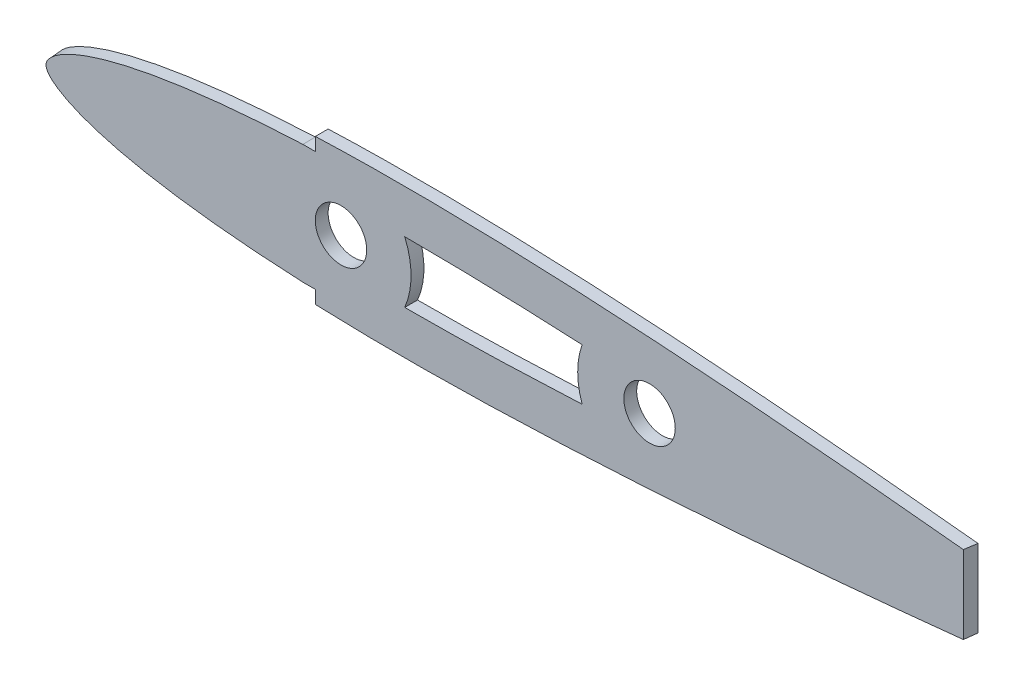
SolidWorks part; units mm, degrees
material "Balsa"
ref_plane "Front Plane" through (0, 0, 0) normal (0, 0, 1) x (1, 0, 0)
ref_plane "Top Plane" through (0, 0, 0) normal (0, 1, 0) x (1, 0, 0)
ref_plane "Right Plane" through (0, 0, 0) normal (1, 0, 0) x (0, 0, -1)
curve "Curve1"
  spline degree 3 poles (306.1523, -0.5171, 0) (306.1523, 0.5171, 0) (305.121, 0.3908, 0) (303.8142, 0.7587, 0) (301.4178, 0.9861, 0) (298.1894, 1.474, 0) (294.0308, 2.0185, 0) (289.0158, 2.6897, 0) (283.1575, 3.4483, 0) (276.4981, 4.2929, 0) (269.0768, 5.2087, 0) (260.9399, 6.1834, 0) (252.1374, 7.2048, 0) (242.7235, 8.259, 0) (232.7563, 9.3331, 0) (222.2974, 10.4139, 0) (211.4111, 11.4873, 0) (200.1646, 12.5383, 0) (188.6272, 13.5531, 0) (176.8702, 14.5147, 0) (164.9658, 15.4075, 0) (152.9874, 16.2149, 0) (141.009, 16.9199, 0) (129.1042, 17.5048, 0) (117.3465, 17.954, 0) (105.8081, 18.2528, 0) (94.5604, 18.3867, 0) (83.6724, 18.345, 0) (73.2112, 18.1196, 0) (63.2413, 17.7049, 0) (53.824, 17.0997, 0) (45.0172, 16.3058, 0) (36.8748, 15.3296, 0) (29.4464, 14.1792, 0) (22.777, 12.8667, 0) (16.9057, 11.407, 0) (11.866, 9.8142, 0) (7.6833, 8.1032, 0) (4.371, 6.2856, 0) (1.9343, 4.3578, 0) (0.3736, 2.2731, 0) (-0.1741, 0, 0) (0.3736, -2.2731, 0) (1.9343, -4.3578, 0) (4.371, -6.2856, 0) (7.6833, -8.1032, 0) (11.866, -9.8142, 0) (16.9057, -11.407, 0) (22.777, -12.8667, 0) (29.4464, -14.1792, 0) (36.8748, -15.3296, 0) (45.0172, -16.3058, 0) (53.824, -17.0997, 0) (63.2413, -17.7049, 0) (73.2112, -18.1196, 0) (83.6724, -18.345, 0) (94.5604, -18.3867, 0) (105.8081, -18.2528, 0) (117.3465, -17.954, 0) (129.1042, -17.5048, 0) (141.009, -16.9199, 0) (152.9874, -16.2149, 0) (164.9658, -15.4075, 0) (176.8702, -14.5147, 0) (188.6272, -13.5531, 0) (200.1646, -12.5383, 0) (211.4111, -11.4873, 0) (222.2974, -10.4139, 0) (232.7563, -9.3331, 0) (242.7235, -8.259, 0) (252.1374, -7.2048, 0) (260.9399, -6.1834, 0) (269.0768, -5.2087, 0) (276.4981, -4.2929, 0) (283.1575, -3.4483, 0) (289.0158, -2.6897, 0) (294.0308, -2.0185, 0) (298.1894, -1.474, 0) (301.4178, -0.9861, 0) (303.8142, -0.7587, 0) (305.121, -0.3908, 0) (306.1523, -0.5171, 0) (306.1523, 0.5171, 0) (305.121, 0.3908, 0) knots -0.004279 -0.001997 -0.001234 0 0.000762 0.003045 0.006832 0.012101 0.018818 0.026939 0.036415 0.047185 0.05918 0.072328 0.086544 0.101741 0.117823 0.134691 0.15224 0.170361 0.188941 0.207865 0.227016 0.246276 0.265525 0.284645 0.30352 0.322035 0.340078 0.357543 0.374325 0.39033 0.405464 0.419644 0.432793 0.444844 0.455738 0.465429 0.473886 0.481102 0.487102 0.491975 0.495931 0.499383 0.502835 0.50679 0.511664 0.517664 0.524879 0.533337 0.543028 0.553922 0.565972 0.579122 0.593302 0.608436 0.62444 0.641223 0.658687 0.676731 0.695245 0.714121 0.733241 0.75249 0.77175 0.7909 0.809825 0.828404 0.846525 0.864074 0.880942 0.897025 0.912222 0.926438 0.939585 0.951581 0.962351 0.971826 0.979948 0.986664 0.991933 0.995721 0.998003 0.998766 1 1.000762 1.003045 1.006832 periodic
sketch "Sketch1" plane through (0, 0, 0) normal (0, 0, 1) x (1, 0, 0)
  spline S0 degree 3 poles (306.1523, -0.5171) (306.1523, 0.5171) (305.121, 0.3908) (303.8142, 0.7587) (301.4178, 0.9861) (298.1894, 1.474) (294.0308, 2.0185) (289.0158, 2.6897) (283.1575, 3.4483) (276.4981, 4.2929) (269.0768, 5.2087) (260.9399, 6.1834) (252.1374, 7.2048) (242.7235, 8.259) (232.7563, 9.3331) (222.2974, 10.4139) (211.4111, 11.4873) (200.1646, 12.5383) (188.6272, 13.5531) (176.8702, 14.5147) (164.9658, 15.4075) (152.9874, 16.2149) (141.009, 16.9199) (129.1042, 17.5048) (117.3465, 17.954) (105.8081, 18.2528) (94.5604, 18.3867) (83.6724, 18.345) (73.2112, 18.1196) (63.2413, 17.7049) (53.824, 17.0997) (45.0172, 16.3058) (36.8748, 15.3296) (29.4464, 14.1792) (22.777, 12.8667) (16.9057, 11.407) (11.866, 9.8142) (7.6833, 8.1032) (4.371, 6.2856) (1.9343, 4.3578) (0.3736, 2.2731) (-0.1741, 0) (0.3736, -2.2731) (1.9343, -4.3578) (4.371, -6.2856) (7.6833, -8.1032) (11.866, -9.8142) (16.9057, -11.407) (22.777, -12.8667) (29.4464, -14.1792) (36.8748, -15.3296) (45.0172, -16.3058) (53.824, -17.0997) (63.2413, -17.7049) (73.2112, -18.1196) (83.6724, -18.345) (94.5604, -18.3867) (105.8081, -18.2528) (117.3465, -17.954) (129.1042, -17.5048) (141.009, -16.9199) (152.9874, -16.2149) (164.9658, -15.4075) (176.8702, -14.5147) (188.6272, -13.5531) (200.1646, -12.5383) (211.4111, -11.4873) (222.2974, -10.4139) (232.7563, -9.3331) (242.7235, -8.259) (252.1374, -7.2048) (260.9399, -6.1834) (269.0768, -5.2087) (276.4981, -4.2929) (283.1575, -3.4483) (289.0158, -2.6897) (294.0308, -2.0185) (298.1894, -1.474) (301.4178, -0.9861) (303.8142, -0.7587) (305.121, -0.3908) (306.1523, -0.5171) (306.1523, 0.5171) (305.121, 0.3908) knots -0.004279 -0.001997 -0.001234 0 0.000762 0.003045 0.006832 0.012101 0.018818 0.026939 0.036415 0.047185 0.05918 0.072328 0.086544 0.101741 0.117823 0.134691 0.15224 0.170361 0.188941 0.207865 0.227016 0.246276 0.265525 0.284645 0.30352 0.322035 0.340078 0.357543 0.374325 0.39033 0.405464 0.419644 0.432793 0.444844 0.455738 0.465429 0.473886 0.481102 0.487102 0.491975 0.495931 0.499383 0.502835 0.50679 0.511664 0.517664 0.524879 0.533337 0.543028 0.553922 0.565972 0.579122 0.593302 0.608436 0.62444 0.641223 0.658687 0.676731 0.695245 0.714121 0.733241 0.75249 0.77175 0.7909 0.809825 0.828404 0.846525 0.864074 0.880942 0.897025 0.912222 0.926438 0.939585 0.951581 0.962351 0.971826 0.979948 0.986664 0.991933 0.995721 0.998003 0.998766 1 1.000762 1.003045 1.006832 only from (305.9684, 0.3855) to (305.9684, 0.3855) construction
  spline S1 degree 3 poles (306.1523, -0.5171) (306.1523, 0.5171) (305.121, 0.3908) (303.8142, 0.7587) (301.4178, 0.9861) (298.1894, 1.474) (294.0308, 2.0185) (289.0158, 2.6897) (283.1575, 3.4483) (276.4981, 4.2929) (269.0768, 5.2087) (260.9399, 6.1834) (252.1374, 7.2048) (242.7235, 8.259) (232.7563, 9.3331) (222.2974, 10.4139) (211.4111, 11.4873) (200.1646, 12.5383) (188.6272, 13.5531) (176.8702, 14.5147) (164.9658, 15.4075) (152.9874, 16.2149) (141.009, 16.9199) (129.1042, 17.5048) (117.3465, 17.954) (105.8081, 18.2528) (94.5604, 18.3867) (83.6724, 18.345) (73.2112, 18.1196) (63.2413, 17.7049) (53.824, 17.0997) (45.0172, 16.3058) (36.8748, 15.3296) (29.4464, 14.1792) (22.777, 12.8667) (16.9057, 11.407) (11.866, 9.8142) (7.6833, 8.1032) (4.371, 6.2856) (1.9343, 4.3578) (0.3736, 2.2731) (-0.1741, 0) (0.3736, -2.2731) (1.9343, -4.3578) (4.371, -6.2856) (7.6833, -8.1032) (11.866, -9.8142) (16.9057, -11.407) (22.777, -12.8667) (29.4464, -14.1792) (36.8748, -15.3296) (45.0172, -16.3058) (53.824, -17.0997) (63.2413, -17.7049) (73.2112, -18.1196) (83.6724, -18.345) (94.5604, -18.3867) (105.8081, -18.2528) (117.3465, -17.954) (129.1042, -17.5048) (141.009, -16.9199) (152.9874, -16.2149) (164.9658, -15.4075) (176.8702, -14.5147) (188.6272, -13.5531) (200.1646, -12.5383) (211.4111, -11.4873) (222.2974, -10.4139) (232.7563, -9.3331) (242.7235, -8.259) (252.1374, -7.2048) (260.9399, -6.1834) (269.0768, -5.2087) (276.4981, -4.2929) (283.1575, -3.4483) (289.0158, -2.6897) (294.0308, -2.0185) (298.1894, -1.474) (301.4178, -0.9861) (303.8142, -0.7587) (305.121, -0.3908) (306.1523, -0.5171) (306.1523, 0.5171) (305.121, 0.3908) knots -0.004279 -0.001997 -0.001234 0 0.000762 0.003045 0.006832 0.012101 0.018818 0.026939 0.036415 0.047185 0.05918 0.072328 0.086544 0.101741 0.117823 0.134691 0.15224 0.170361 0.188941 0.207865 0.227016 0.246276 0.265525 0.284645 0.30352 0.322035 0.340078 0.357543 0.374325 0.39033 0.405464 0.419644 0.432793 0.444844 0.455738 0.465429 0.473886 0.481102 0.487102 0.491975 0.495931 0.499383 0.502835 0.50679 0.511664 0.517664 0.524879 0.533337 0.543028 0.553922 0.565972 0.579122 0.593302 0.608436 0.62444 0.641223 0.658687 0.676731 0.695245 0.714121 0.733241 0.75249 0.77175 0.7909 0.809825 0.828404 0.846525 0.864074 0.880942 0.897025 0.912222 0.926438 0.939585 0.951581 0.962351 0.971826 0.979948 0.986664 0.991933 0.995721 0.998003 0.998766 1 1.000762 1.003045 1.006832 only from (305.9684, 0.3855) to (305.9684, 0.3855)
extrude "Boss-Extrude1" add sketch "Sketch1" along normal blind 3.175
sketch "Sketch2" plane through (0, 0, 3.175) normal (0, 0, 1) x (1, 0, 0)
  circle A0 centre (76.2, 0) radius 6.35
  circle A1 centre (152.4, 0) radius 6.35
  dimension "D1" = 12.7
  dimension "D2" = 12.7
  dimension "D3" = 0
  dimension "D4" = 0
  dimension "D5" = 76.2
  dimension "D6" = 152.4
extrude "Cut-Extrude1" cut sketch "Sketch2" against normal blind 3.175
sketch "Sketch3" plane through (0, 0, 0) normal (0, 1, 0) x (1, 0, 0)
  line L1 (230.3394, 0) -> (229.8928, -3.175)
  line L4 (0, -3.175) -> (306.1063, -3.175) construction
  line L5 (229.8928, -3.175) -> (306.1063, -3.175)
  line L6 (0, 0) -> (306.1063, 0) construction
  line L7 (230.3394, 0) -> (306.1063, 0)
  line L8 (306.1063, -3.175) -> (306.1063, 0) construction
  line L9 (306.1063, -3.175) -> (306.1063, 0)
extrude "Cut-Extrude2" cut sketch "Sketch3" against normal through all both and the other way through all
sketch "Sketch4" plane through (0, 0, 0) normal (0, 0, -1) x (-1, 0, 0)
  line L0 (-69.85, 14.6757) -> (-69.85, 17.9856)
  line L1 (-69.85, 14.6757) -> (-69.85, 17.9856)
  line L2 (-69.85, -17.9856) -> (-69.85, -14.6757)
  line L3 (-69.85, -17.9856) -> (-69.85, -14.6757)
  line L4 (-69.85, -14.6757) -> (-66.675, -14.6757)
  line L5 (-69.85, -14.6757) -> (-66.675, -14.6757)
  line L6 (-66.675, 14.6757) -> (-69.85, 14.6757)
  line L7 (-66.675, 14.6757) -> (-69.85, 14.6757)
  line L9 (14.9553, 25.8479) -> (7.0772, -39.7459)
  line L11 (-69.85, -17.9856) -> (-69.85, -24.7094)
  line L12 (-69.85, -24.7094) -> (7.0772, -39.7459)
  line L13 (-69.85, 17.9856) -> (-69.85, 25.8479)
  line L14 (-69.85, 25.8479) -> (14.9553, 25.8479)
  spline S0 degree 3 poles (-525.673, 1919.933) (-507.4305, -166.7217) (-268.0706, 33.0376) (-47.1243, 13.3223) (-44.3402, 13.0374) (-38.7807, 12.3781) (-36.0052, 12.0037) (-31.8507, 11.3535) (-30.4676, 11.1222) (-27.7086, 10.6247) (-26.3327, 10.3585) (-23.5918, 9.7853) (-20.8602, 9.1726) (-18.1539, 8.4532) (-15.4635, 7.6665) (-14.1234, 7.2372) (-11.4846, 6.2836) (-10.186, 5.7609) (-8.2916, 4.8593) (-7.6688, 4.5398) (-6.7555, 4.0149) (-6.4546, 3.8323) (-5.8614, 3.4481) (-5.5692, 3.2471) (-5.0031, 2.8232) (-4.7279, 2.5992) (-4.2064, 2.1212) (-3.96, 1.869) (-3.5148, 1.3218) (-3.3126, 1.0237) (-3.1166, 0.5278) (-3.0687, 0.3551) (-3.0372, 0.0912) (-3.034, 0.001) (-3.0452, -0.1764) (-3.0583, -0.2639) (-3.0958, -0.4367) (-3.1449, -0.6079) (-3.2134, -0.7723) (-3.3276, -1.011) (-3.419, -1.1619) (-3.6214, -1.4535) (-3.7307, -1.5922) (-3.9606, -1.8584) (-4.0811, -1.9861) (-4.4525, -2.3571) (-4.7159, -2.5879) (-5.2651, -3.0261) (-5.5514, -3.2337) (-6.4218, -3.8246) (-7.0213, -4.1796) (-8.246, -4.8385) (-8.8709, -5.1428) (-10.1374, -5.7174) (-10.7796, -5.9869) (-12.0778, -6.4979) (-12.7347, -6.7399) (-14.0517, -7.2) (-14.7125, -7.418) (-16.0381, -7.834) (-16.7028, -8.032) (-18.7018, -8.6015) (-21.3796, -9.2971) (-24.0773, -9.891) (-28.1349, -10.725) (-30.8553, -11.2025) (-36.3175, -12.0473) (-39.0594, -12.4138) (-44.5599, -13.0607) (-47.3197, -13.3412) (-267.3718, -32.8588) (-500.1956, 164.9438) (-570.4368, -1909.3501) knots -4.766283 -4.766283 -4.766283 -4.766283 0.125 0.125 0.1875 0.1875 0.25 0.25 0.28125 0.28125 0.3125 0.3125 0.34375 0.375 0.375 0.40625 0.40625 0.4375 0.4375 0.453125 0.453125 0.460938 0.460938 0.46875 0.46875 0.476563 0.476563 0.484375 0.484375 0.492188 0.492188 0.496094 0.496094 0.498047 0.498047 0.5 0.5 0.501953 0.503906 0.503906 0.507813 0.507813 0.511719 0.511719 0.515625 0.515625 0.523438 0.523438 0.53125 0.53125 0.546875 0.546875 0.5625 0.5625 0.578125 0.578125 0.59375 0.59375 0.609375 0.609375 0.625 0.625 0.65625 0.6875 0.6875 0.75 0.75 0.8125 0.8125 0.875 0.875 5.793459 5.793459 5.793459 5.793459 only from (-66.675, 14.6757) to (-66.675, -14.6757)
  spline S1 degree 3 poles (-66.675, 14.6757) (-61.0762, 14.4228) (-55.4871, 14.0685) (-47.1243, 13.3223) (-44.3402, 13.0374) (-38.7807, 12.3781) (-36.0052, 12.0037) (-31.8507, 11.3535) (-30.4676, 11.1222) (-27.7086, 10.6247) (-26.3327, 10.3585) (-23.5918, 9.7853) (-20.8602, 9.1726) (-18.1539, 8.4532) (-15.4635, 7.6665) (-14.1234, 7.2372) (-11.4846, 6.2836) (-10.186, 5.7609) (-8.2916, 4.8593) (-7.6688, 4.5398) (-6.7555, 4.0149) (-6.4546, 3.8323) (-5.8614, 3.4481) (-5.5692, 3.2471) (-5.0031, 2.8232) (-4.7279, 2.5992) (-4.2064, 2.1212) (-3.96, 1.869) (-3.5148, 1.3218) (-3.3126, 1.0237) (-3.1166, 0.5278) (-3.0687, 0.3551) (-3.0372, 0.0912) (-3.034, 0.001) (-3.0452, -0.1764) (-3.0583, -0.2639) (-3.0958, -0.4367) (-3.1449, -0.6079) (-3.2134, -0.7723) (-3.3276, -1.011) (-3.419, -1.1619) (-3.6214, -1.4535) (-3.7307, -1.5922) (-3.9606, -1.8584) (-4.0811, -1.9861) (-4.4525, -2.3571) (-4.7159, -2.5879) (-5.2651, -3.0261) (-5.5514, -3.2337) (-6.4218, -3.8246) (-7.0213, -4.1796) (-8.246, -4.8385) (-8.8709, -5.1428) (-10.1374, -5.7174) (-10.7796, -5.9869) (-12.0778, -6.4979) (-12.7347, -6.7399) (-14.0517, -7.2) (-14.7125, -7.418) (-16.0381, -7.834) (-16.7028, -8.032) (-18.7018, -8.6015) (-21.3796, -9.2971) (-24.0773, -9.891) (-28.1349, -10.725) (-30.8553, -11.2025) (-36.3175, -12.0473) (-39.0594, -12.4138) (-44.5599, -13.0607) (-47.3197, -13.3412) (-55.6032, -14.0759) (-61.1355, -14.4255) (-66.675, -14.6757) knots 0 0 0 0 0.125 0.125 0.1875 0.1875 0.25 0.25 0.28125 0.28125 0.3125 0.3125 0.34375 0.375 0.375 0.40625 0.40625 0.4375 0.4375 0.453125 0.453125 0.460938 0.460938 0.46875 0.46875 0.476563 0.476563 0.484375 0.484375 0.492188 0.492188 0.496094 0.496094 0.498047 0.498047 0.5 0.5 0.501953 0.503906 0.503906 0.507813 0.507813 0.511719 0.511719 0.515625 0.515625 0.523438 0.523438 0.53125 0.53125 0.546875 0.546875 0.5625 0.5625 0.578125 0.578125 0.59375 0.59375 0.609375 0.609375 0.625 0.625 0.65625 0.6875 0.6875 0.75 0.75 0.8125 0.8125 0.875 0.875 1 1 1 1
sketch "Sketch6" plane through (0, 0, 3.175) normal (0, 0, 1) x (1, 0, 0)
  line L0 (69.85, -17.9195) -> (69.85, -14.7386)
  line L1 (69.85, -17.9195) -> (69.85, -14.7386)
  line L2 (66.802, -14.7386) -> (69.85, -14.7386)
  line L3 (66.802, -14.7386) -> (69.85, -14.7386)
  line L4 (69.85, 14.7386) -> (69.85, 17.9195)
  line L5 (69.85, 14.7386) -> (69.85, 17.9195)
  line L6 (69.85, 14.7386) -> (66.802, 14.7386)
  line L7 (69.85, 14.7386) -> (66.802, 14.7386)
  line L9 (-20.5382, 29.7745) -> (-2.2039, -44.3312)
  line L11 (69.85, 17.9195) -> (69.85, 27.9076)
  line L12 (69.85, 27.9076) -> (-20.5382, 29.7745)
  line L13 (69.85, -17.9195) -> (69.85, -31.725)
  line L15 (-2.2039, -44.3312) -> (69.85, -31.725)
  spline S0 degree 3 poles (-1346.6934, 1419.9435) (497.4511, -122.9147) (271.935, 27.2917) (57.9529, 14.254) (53.5379, 13.9335) (49.1319, 13.557) (44.735, 13.1191) (40.3523, 12.6122) (35.9847, 12.0284) (32.3657, 11.4684) (29.482, 10.9698) (27.3293, 10.5683) (25.1865, 10.1362) (23.0568, 9.671) (20.9414, 9.17) (18.8445, 8.6282) (16.7702, 8.0408) (14.7254, 7.4009) (12.7203, 6.7032) (10.7669, 5.9336) (8.8873, 5.0828) (7.1222, 4.1415) (5.7955, 3.2682) (4.8814, 2.5212) (4.2998, 1.9523) (3.832, 1.3773) (3.5401, 0.8783) (3.3766, 0.3988) (3.3284, 0) (3.3766, -0.3988) (3.5401, -0.8783) (3.832, -1.3773) (4.2998, -1.9523) (4.8814, -2.5212) (5.7959, -3.2685) (7.122, -4.1413) (8.8874, -5.0829) (10.7668, -5.9335) (12.7204, -6.7033) (14.7254, -7.4009) (16.7702, -8.0408) (18.8444, -8.6282) (20.9414, -9.17) (23.0568, -9.671) (25.1866, -10.1362) (27.3293, -10.5683) (29.482, -10.9698) (32.3658, -11.4684) (35.9846, -12.0283) (40.3524, -12.6122) (44.735, -13.1191) (49.1319, -13.557) (53.5379, -13.9335) (57.9529, -14.254) (271.7682, -27.2815) (497.1332, 122.6753) (-1351.4434, -1415.2138) knots -4.442135 -4.442135 -4.442135 -4.442135 0.03125 0.0625 0.09375 0.125 0.15625 0.1875 0.21875 0.25 0.265625 0.28125 0.296875 0.3125 0.328125 0.34375 0.359375 0.375 0.390625 0.40625 0.421875 0.4375 0.453125 0.460938 0.46875 0.476562 0.484375 0.492188 0.5 0.507812 0.515625 0.523438 0.53125 0.539062 0.546875 0.5625 0.578125 0.59375 0.609375 0.625 0.640625 0.65625 0.671875 0.6875 0.703125 0.71875 0.734375 0.75 0.78125 0.8125 0.84375 0.875 0.90625 0.9375 0.96875 5.438604 5.438604 5.438604 5.438604 only from (66.802, 14.7386) to (66.802, -14.7386)
  spline S1 degree 3 poles (66.802, 14.7386) (65.3266, 14.6717) (62.3756, 14.5234) (57.9529, 14.254) (53.5379, 13.9335) (49.1319, 13.557) (44.735, 13.1191) (40.3523, 12.6122) (35.9847, 12.0284) (32.3657, 11.4684) (29.482, 10.9698) (27.3293, 10.5683) (25.1865, 10.1362) (23.0568, 9.671) (20.9414, 9.17) (18.8445, 8.6282) (16.7702, 8.0408) (14.7254, 7.4009) (12.7203, 6.7032) (10.7669, 5.9336) (8.8873, 5.0828) (7.1222, 4.1415) (5.7955, 3.2682) (4.8814, 2.5212) (4.2998, 1.9523) (3.832, 1.3773) (3.5401, 0.8783) (3.3766, 0.3988) (3.3284, 0) (3.3766, -0.3988) (3.5401, -0.8783) (3.832, -1.3773) (4.2998, -1.9523) (4.8814, -2.5212) (5.7959, -3.2685) (7.122, -4.1413) (8.8874, -5.0829) (10.7668, -5.9335) (12.7204, -6.7033) (14.7254, -7.4009) (16.7702, -8.0408) (18.8444, -8.6282) (20.9414, -9.17) (23.0568, -9.671) (25.1866, -10.1362) (27.3293, -10.5683) (29.482, -10.9698) (32.3658, -11.4684) (35.9846, -12.0283) (40.3524, -12.6122) (44.735, -13.1191) (49.1319, -13.557) (53.5379, -13.9335) (57.9529, -14.254) (62.3756, -14.5234) (65.3266, -14.6717) (66.802, -14.7386) knots 0 0 0 0 0.03125 0.0625 0.09375 0.125 0.15625 0.1875 0.21875 0.25 0.265625 0.28125 0.296875 0.3125 0.328125 0.34375 0.359375 0.375 0.390625 0.40625 0.421875 0.4375 0.453125 0.460938 0.46875 0.476562 0.484375 0.492188 0.5 0.507812 0.515625 0.523438 0.53125 0.539062 0.546875 0.5625 0.578125 0.59375 0.609375 0.625 0.640625 0.65625 0.671875 0.6875 0.703125 0.71875 0.734375 0.75 0.78125 0.8125 0.84375 0.875 0.90625 0.9375 0.96875 1 1 1 1
loft "Cut-Loft1" cut profiles "Sketch6", "Sketch4"
sketch "Sketch7" plane through (0, 0, 0) normal (0, 0, -1) x (-1, 0, 0)
  arc A3 (-91.9307, 7.5684) -> (-91.9307, -7.5684) centre (-74.4487, 0) ccw
  arc A12 (-135.7496, -6.3647) -> (-135.7496, 6.3647) centre (-153.705, 0) ccw
  spline S0 degree 3 poles (-135.7496, 6.3647) (-132.3022, 6.5373) (-128.8558, 6.6944) (-119.2563, 7.0844) (-113.1061, 7.2797) (-101.9469, 7.5096) (-96.9345, 7.5671) (-91.9307, 7.5684) knots 0.555031 0.555031 0.555031 0.555031 0.625 0.625 0.75 0.75 0.852123 0.852123 0.852123 0.852123
  spline S9 degree 3 poles (-492.7525, 2902.4427) (423.1928, 162.9563) (179.9734, -6.2507) (-94.6891, -7.5906) (-100.8229, -7.5328) (-113.1061, -7.2797) (-119.2563, -7.0844) (-131.5653, -6.5843) (-137.7242, -6.2795) (-156.2087, -5.2298) (-168.5429, -4.3532) (-826.8817, 49.0637) (-1475.1475, 444.686) (-1030.6868, -2394.1733) knots -5.360135 -5.360135 -5.360135 -5.360135 0.125 0.125 0.25 0.25 0.375 0.375 0.5 0.5 0.75 0.75 13.844903 13.844903 13.844903 13.844903 only from (-70.2628, -7.1812) to (-217.8704, 0)
  spline S10 degree 3 poles (-1030.6781, 2394.229) (-1475.156, -444.6912) (-826.8859, -49.064) (-168.5429, 4.3532) (-156.2087, 5.2298) (-137.7242, 6.2795) (-131.5653, 6.5843) (-119.2563, 7.0844) (-113.1061, 7.2797) (-100.8229, 7.5328) (-94.6891, 7.5906) (179.9668, 6.2508) (423.1808, -162.9479) (-492.6845, -2902.2395) knots -12.844989 -12.844989 -12.844989 -12.844989 0.25 0.25 0.5 0.5 0.625 0.625 0.75 0.75 0.875 0.875 6.359999 6.359999 6.359999 6.359999 only from (-217.8704, 0) to (-70.2628, 7.1812)
  spline S11 degree 3 poles (-91.9307, -7.5684) (-96.9345, -7.5671) (-101.9469, -7.5096) (-113.1061, -7.2797) (-119.2563, -7.0844) (-128.8558, -6.6944) (-132.3022, -6.5373) (-135.7496, -6.3647) knots 0.147877 0.147877 0.147877 0.147877 0.25 0.25 0.375 0.375 0.444969 0.444969 0.444969 0.444969
  dimension "D1" = 10.795
extrude "Cut-Extrude4" cut sketch "Sketch7" against normal blind 7.62
